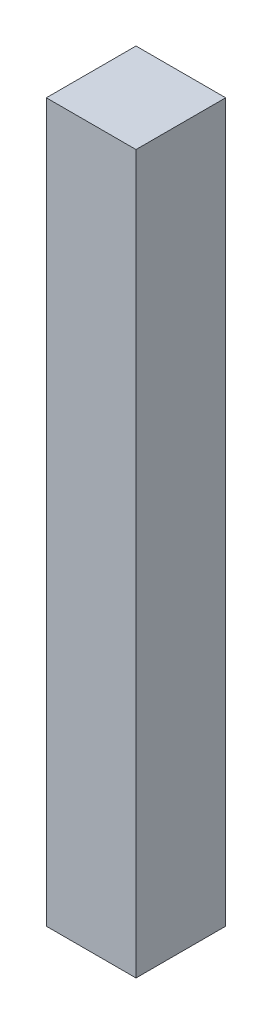
SolidWorks part; units mm, degrees
ref_plane "Front Plane" through (0, 0, 0) normal (0, 0, 1) x (1, 0, 0)
ref_plane "Top Plane" through (0, 0, 0) normal (0, 1, 0) x (1, 0, 0)
ref_plane "Right Plane" through (0, 0, 0) normal (1, 0, 0) x (0, 0, -1)
sketch "Sketch2" plane through (0, 0, 0) normal (0, 0, 1) x (1, 0, 0)
  line L1 (-1.5875, -12.7025) -> (1.5875, -12.7025)
  line L2 (-1.5875, -12.7025) -> (-1.5875, 12.7025)
  line L3 (-1.5875, 12.7025) -> (1.5875, 12.7025)
  line L4 (1.5875, -12.7025) -> (1.5875, 12.7025)
  line L5 (-1.5875, -12.7025) -> (1.5875, 12.7025) construction
  line L6 (-1.5875, 12.7025) -> (1.5875, -12.7025) construction
  point P0 (0, 0)
  dimension "D1" = 3.175
  dimension "D2" = 25.4051
extrude "Boss-Extrude1" add sketch "Sketch2" along normal blind 3.175
equation "\"side thickness\"= 1 / 8in"
equation "\"extrude thickness\"= 1 / 8in"
equation "\"length\"= 0.9522 + 0.048in"
equation "\"D1@Sketch2\"=\"side thickness\""
equation "\"D2@Sketch2\"=\"length\""
equation "\"D1@Boss-Extrude1\"=\"extrude thickness\""
